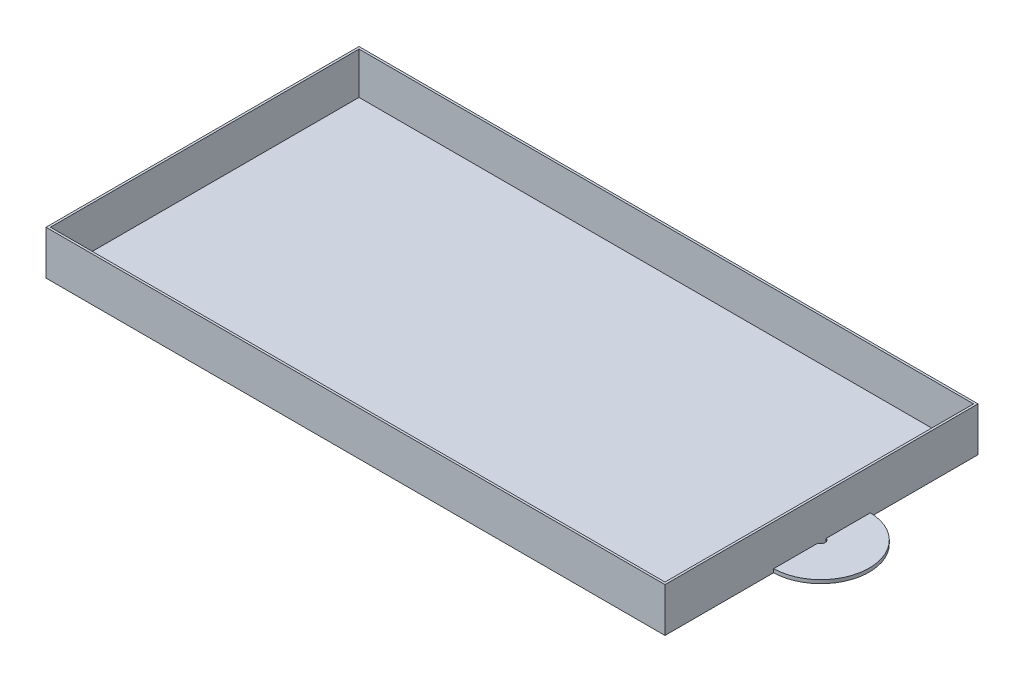
SolidWorks part; units mm, degrees
ref_plane "Alzado" through (0, 0, 0) normal (0, 0, 1) x (1, 0, 0)
ref_plane "Planta" through (0, 0, 0) normal (0, 1, 0) x (1, 0, 0)
ref_plane "Vista lateral" through (0, 0, 0) normal (1, 0, 0) x (0, 0, -1)
sketch "Croquis1" plane through (0, 0, 0) normal (0, 1, 0) x (1, 0, 0)
  line L1 (0, 2.6074) -> (-140.3961, 2.6074)
  line L2 (0, 2.6074) -> (0, -68.393)
  line L3 (0, -68.393) -> (-140.3961, -68.393)
  line L4 (-140.3961, 2.6074) -> (-140.3961, -68.393)
extrude "Saliente-Extruir1" add sketch "Croquis1" along normal blind 10
shell "Vaciado1" thickness 0.5
sketch "Croquis2" plane through (0, 0, 0) normal (0, 1, 0) x (1, 0, 0)
  line L0 (-0.5, -67.893) -> (-0.5, 2.1074) construction
  line L1 (0, -68.393) -> (0, 2.6074) construction
  arc A0 (-0.5, -21.8067) -> (0, -43.7549) centre (-0.25, -32.7808) cw
extrude "Extruir-Lámina1" add sketch "Croquis2" along normal blind 0.8 thin
